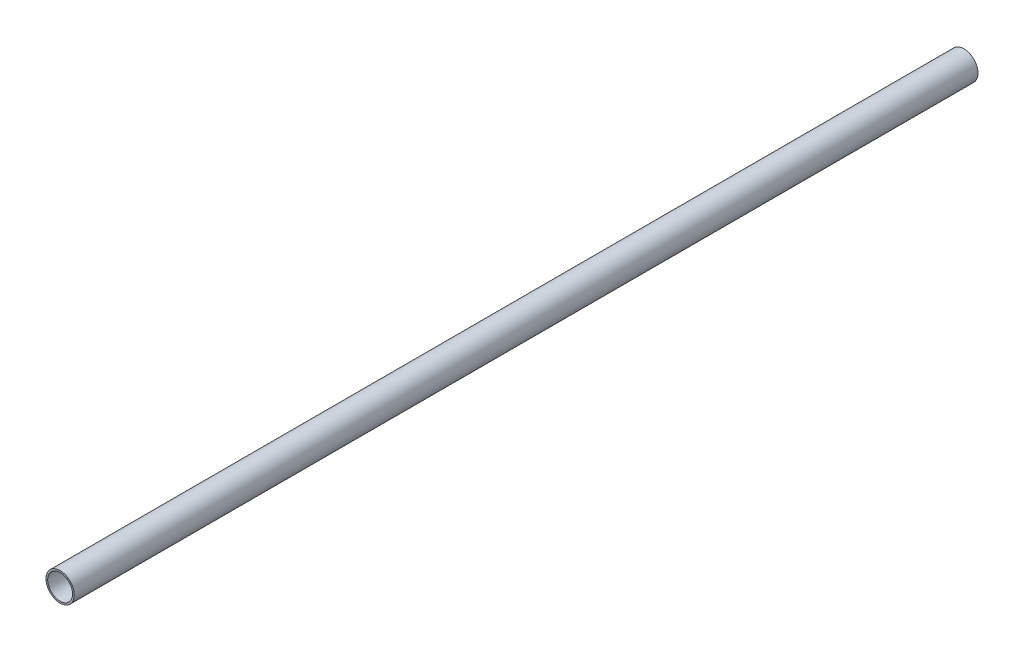
SolidWorks part; units mm, degrees
material "Carbon Fiber Tube - UD Approx"
ref_plane "Front Plane" through (0, 0, 0) normal (0, 0, 1) x (1, 0, 0)
ref_plane "Top Plane" through (0, 0, 0) normal (0, 1, 0) x (1, 0, 0)
ref_plane "Right Plane" through (0, 0, 0) normal (1, 0, 0) x (0, 0, -1)
sketch "Sketch1" plane through (0, 0, 0) normal (0, 0, 1) x (1, 0, 0)
  circle A0 centre (0, 0) radius 12.5
  circle A1 centre (0, 0) radius 11
  dimension "D1" = 25
  dimension "D2" = 22
extrude "Boss-Extrude1" add sketch "Sketch1" along normal blind 800
